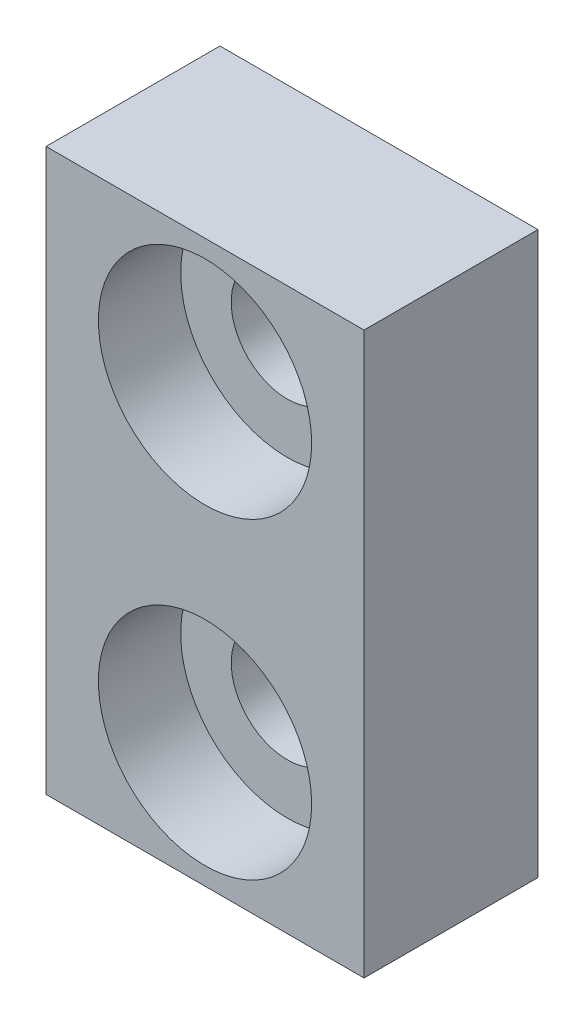
SolidWorks part; units mm, degrees
ref_plane "Front" through (0, 0, 0) normal (0, 0, 1) x (1, 0, 0)
ref_plane "Top" through (0, 0, 0) normal (0, 1, 0) x (1, 0, 0)
ref_plane "Right" through (0, 0, 0) normal (1, 0, 0) x (0, 0, -1)
sketch "Sketch1" plane through (0, 0, 0) normal (0, 0, 1) x (1, 0, 0)
  line L1 (-4.25, -7.5) -> (4.25, -7.5)
  line L2 (-4.25, -7.5) -> (-4.25, 7.5)
  line L3 (-4.25, 7.5) -> (4.25, 7.5)
  line L4 (4.25, -7.5) -> (4.25, 7.5)
  line L5 (-4.25, -7.5) -> (4.25, 7.5) construction
  line L6 (-4.25, 7.5) -> (4.25, -7.5) construction
  point P0 (0, 0)
  dimension "D1" = 15
  dimension "D2" = 8.5
extrude "Boss-Extrude1" add sketch "Sketch1" along normal blind 4.65
sketch "Sketch2" plane through (0, 0, 4.65) normal (0, 0, 1) x (1, 0, 0)
  line L0 (0, -7.5) -> (0, -4.175)
  line L1 (-4.25, -7.5) -> (4.25, -7.5) construction
  line L2 (0, 7.5) -> (0, 4.175)
  line L3 (4.25, 7.5) -> (-4.25, 7.5) construction
  circle A0 centre (0, -4.175) radius 2.85
  circle A1 centre (0, 4.175) radius 2.85
  dimension "D1" = 3.325
  dimension "D2" = 3.325
hole_wizard "Ø3.0mm Dowel Hole1" positions "Sketch3" profile "Sketch5" hole size "Ø3.0" standard "ANSI Metric"
sketch "Sketch3" plane through (0, 0, 4.65) normal (0, 0, 1) x (1, 0, 0)
  point P0 (0, 4.175)
  point P3 (0, -4.175)
sketch "Sketch5" plane through (0, 4.175, 4.65) normal (1, 0, 0) x (0, -1, 0)
  line L0 (0, 0) -> (0, 5.9013)
  line L1 (0, 5.9013) -> (1.5, 5)
  line L2 (1.5, 5) -> (1.5, 0)
  line L5 (1.5, 0) -> (0, 0)
  line L10 (0, 5.9013) -> (-1.5, 5) construction
  line L11 (0, -6.35) -> (0, 107.95) construction
  dimension "Hole Dia." = 3
  dimension "Hole Depth" = 5
  dimension "Drill Angle" = 118
extrude "Cut-Extrude2" cut sketch "Sketch2" against normal blind 2.2 contours A1 | A0
